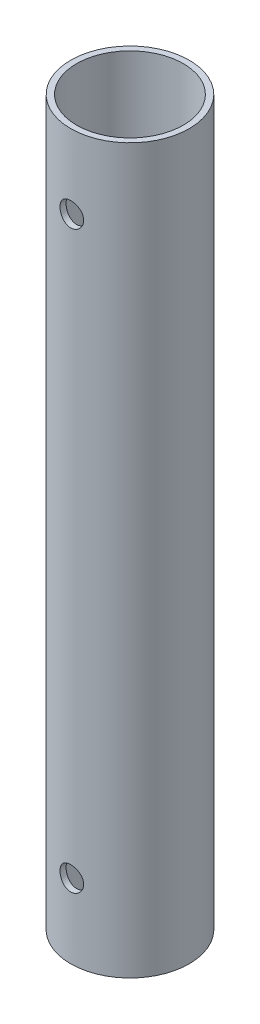
SolidWorks part; units mm, degrees
ref_plane "Front" through (0, 0, 0) normal (0, 0, 1) x (1, 0, 0)
ref_plane "Top" through (0, 0, 0) normal (0, 1, 0) x (1, 0, 0)
ref_plane "Right" through (0, 0, 0) normal (1, 0, 0) x (0, 0, -1)
sketch "Sketch1" plane through (0, 0, 0) normal (0, 1, 0) x (1, 0, 0)
  circle A0 centre (0, 0) radius 10
  circle A1 centre (0, 0) radius 9
  dimension "D1" = 20
  dimension "D2" = 1
extrude "Boss-Extrude1" add sketch "Sketch1" along normal blind 122
ref_plane "Plane1" through (0, 0, 10) normal (0, 0, 1) x (1, 0, 0)
sketch "Sketch3" plane through (0, 0, 10) normal (0, 0, 1) x (1, 0, 0)
  line L0 (0, 122) -> (0, 109.5) construction
  line L1 (10, 122) -> (-10, 122) construction
  line L2 (0, 0) -> (0, 12.5) construction
  circle A0 centre (0, 109.5) radius 2
  circle A1 centre (0, 12.5) radius 2
  dimension "D3" = 4
  dimension "D4" = 4
  dimension "D1" = 12.5
  dimension "D2" = 12.5
extrude "Cut-Extrude2" cut sketch "Sketch3" against normal through all
